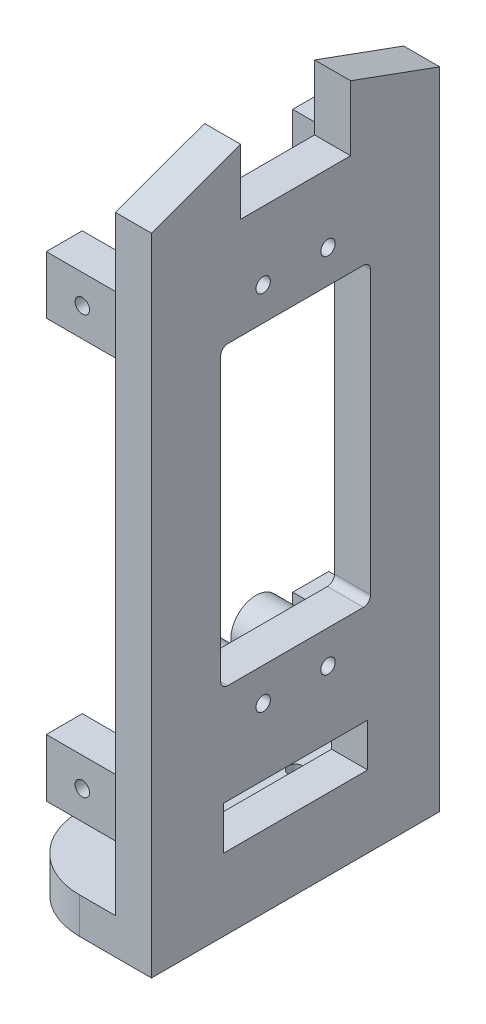
SolidWorks part; units mm, degrees
ref_plane "Front Plane" through (0, 0, 0) normal (0, 0, 1) x (1, 0, 0)
ref_plane "Top Plane" through (0, 0, 0) normal (0, 1, 0) x (1, 0, 0)
ref_plane "Right Plane" through (0, 0, 0) normal (1, 0, 0) x (0, 0, -1)
sketch "Sketch1" plane through (0, 0, 0) normal (0, 1, 0) x (1, 0, 0)
  line L0 (5.3196, -11.3329) -> (15.3196, -11.3329)
  line L1 (15.3196, -11.3329) -> (15.3196, 28.6671)
  line L2 (15.3196, 28.6671) -> (5.3196, 28.6671)
  line L3 (-4.6804, 18.6671) -> (-4.6804, -1.3329)
  arc A0 (5.3196, 28.6671) -> (-4.6804, 18.6671) centre (5.3196, 18.6671) ccw
  arc A1 (-4.6804, -1.3329) -> (5.3196, -11.3329) centre (5.3196, -1.3329) ccw
  circle A2 centre (5.3196, 18.6671) radius 1
  circle A3 centre (5.3196, -1.3329) radius 1
extrude "Boss-Extrude1" add sketch "Sketch1" along normal blind 5
sketch "Sketch2" plane through (0, 5, 0) normal (0, 1, 0) x (1, 0, 0)
  line L0 (15.3196, 28.6671) -> (15.3196, -11.3329)
  line L1 (15.3196, 28.6671) -> (10.3196, 28.6671)
  line L2 (15.3196, -11.3329) -> (10.3196, -11.3329)
  line L3 (10.3196, 28.6671) -> (10.3196, -11.3329)
  dimension "D1" = 5
extrude "Boss-Extrude2" add sketch "Sketch2" along normal blind 80
sketch "Sketch3" plane through (10.3196, 0, 0) normal (-1, 0, 0) x (0, 0, 1)
  line L0 (-8.6671, 85) -> (-8.6671, 5) construction
  line L1 (-28.6671, 85) -> (11.3329, 85) construction
  line L2 (-18.6671, 5) -> (1.3329, 5) construction
  line L4 (1.3329, 36.402) -> (1.3329, 60.5442)
  line L5 (-18.0671, 35.802) -> (0.7329, 35.802)
  line L7 (-18.6671, 60.5442) -> (-18.6671, 36.402)
  line L10 (-18.6671, 69.9442) -> (-18.6671, 60.5442)
  line L11 (-8.6671, 70.5442) -> (-12.0788, 70.5442)
  line L12 (-12.0788, 70.5442) -> (-18.0671, 70.5442)
  line L14 (-5.2553, 70.5442) -> (-8.6671, 70.5442)
  line L16 (0.7329, 70.5442) -> (-5.2553, 70.5442)
  line L17 (1.3329, 60.5442) -> (1.3329, 69.9442)
  line L19 (1.7329, 36.402) -> (1.7329, 60.5442)
  line L20 (1.7329, 60.5442) -> (1.7329, 69.9442)
  line L21 (0.7329, 70.9442) -> (-5.2553, 70.9442)
  line L22 (-5.2553, 70.9442) -> (-8.6671, 70.9442)
  line L23 (-8.6671, 70.9442) -> (-12.0788, 70.9442)
  line L24 (-12.0788, 70.9442) -> (-18.0671, 70.9442)
  line L25 (-19.0671, 69.9442) -> (-19.0671, 60.5442)
  line L26 (-19.0671, 60.5442) -> (-19.0671, 36.402)
  line L27 (-18.0671, 35.402) -> (0.7329, 35.402)
  arc A1 (0.7329, 35.802) -> (1.3329, 36.402) centre (0.7329, 36.402) ccw
  arc A2 (-18.6671, 36.402) -> (-18.0671, 35.802) centre (-18.0671, 36.402) ccw
  arc A5 (-18.0671, 70.5442) -> (-18.6671, 69.9442) centre (-18.0671, 69.9442) ccw
  arc A8 (1.3329, 69.9442) -> (0.7329, 70.5442) centre (0.7329, 69.9442) ccw
  arc A10 (-15.1231, 76.5942) -> (-11.2111, 76.5942) centre (-13.1671, 75.5442) ccw
  arc A11 (-11.2111, 24.1942) -> (-15.1231, 24.1942) centre (-13.1671, 25.2442) ccw
  arc A12 (-2.2111, 24.1942) -> (-6.1231, 24.1942) centre (-4.1671, 25.2442) ccw
  arc A13 (-6.1231, 76.5942) -> (-2.2111, 76.5942) centre (-4.1671, 75.5442) ccw
  arc A14 (1.7329, 69.9442) -> (0.7329, 70.9442) centre (0.7329, 69.9442) ccw
  arc A15 (-18.0671, 70.9442) -> (-19.0671, 69.9442) centre (-18.0671, 69.9442) ccw
  arc A16 (-19.0671, 36.402) -> (-18.0671, 35.402) centre (-18.0671, 36.402) ccw
  arc A17 (0.7329, 35.402) -> (1.7329, 36.402) centre (0.7329, 36.402) ccw
  circle A18 centre (-13.1671, 25.2442) radius 2.22
  circle A19 centre (-4.1671, 25.2442) radius 2.22
  circle A20 centre (-13.1671, 75.5442) radius 2.22
  circle A21 centre (-4.1671, 75.5442) radius 2.22
  dimension "D1" = 0.4
extrude "Cut-Extrude3" cut sketch "Sketch3" against normal blind 80 contours A12 A19 | A11 A18 | L0 L11 L12 A5 L10 L7 A2 L5 | L14 L0 L5 A1 L4 L17 A8 L16 | L0 L23 L24 A15 L25 L26 A16 L27 L5 A2 L7 L10 A5 L12 L11 | L22 L0 L14 L16 A8 L17 L4 A1 L5 L27 A17 L19 L20 A14 L21 | A13 A21 | A10 A20
sketch "Sketch5" plane through (15.3196, 0, 0) normal (1, 0, 0) x (0, 0, -1)
  circle A0 centre (4.1671, 25.2442) radius 2.22 construction
  circle A1 centre (13.1671, 25.2442) radius 2.22 construction
  circle A2 centre (4.1671, 75.5442) radius 2.22 construction
  circle A3 centre (13.1671, 75.5442) radius 2.22 construction
  circle A4 centre (4.1671, 25.2442) radius 2.22
  circle A5 centre (13.1671, 25.2442) radius 2.22
  circle A6 centre (4.1671, 75.5442) radius 2.22
  circle A7 centre (13.1671, 75.5442) radius 2.22
  circle A8 centre (4.1671, 75.5442) radius 1
  circle A9 centre (13.1671, 75.5442) radius 1
  circle A10 centre (13.1671, 25.2442) radius 1
  circle A11 centre (4.1671, 25.2442) radius 1
  dimension "D1" = 2
  dimension "D2" = 2
  dimension "D3" = 2
  dimension "D4" = 2
extrude "Boss-Extrude3" add sketch "Sketch5" against normal blind 10
sketch "Sketch6" plane through (10.3196, 0, 0) normal (-1, 0, 0) x (0, 0, 1)
  circle A0 centre (-4.1671, 25.2442) radius 3.5
  circle A1 centre (-13.1671, 25.2442) radius 3.5
  circle A2 centre (-4.1671, 75.5442) radius 3.5
  circle A3 centre (-13.1671, 75.5442) radius 3.5
  circle A4 centre (-13.1671, 25.2442) radius 2.22 construction
  circle A5 centre (-4.1671, 25.2442) radius 2.22 construction
  circle A6 centre (-4.1671, 75.5442) radius 2.22 construction
  circle A7 centre (-13.1671, 75.5442) radius 2.22 construction
  circle A8 centre (-13.1671, 25.2442) radius 2.22
  circle A9 centre (-4.1671, 25.2442) radius 2.22
  circle A10 centre (-4.1671, 75.5442) radius 2.22
  circle A11 centre (-13.1671, 75.5442) radius 2.22
  dimension "D1" = 7
extrude "Boss-Extrude4" add sketch "Sketch6" along normal up to surface (5 mm away) up to face at (5.3196, 25.2442, -5.1671)
sketch "Sketch7" plane through (10.3196, 0, 0) normal (-1, 0, 0) x (0, 0, 1)
  line L0 (0.7329, 57.1325) -> (0.7329, 36.402)
  line L1 (1.3329, 36.402) -> (1.3329, 60.5442)
  line L2 (-18.0671, 35.802) -> (0.7329, 35.802)
  line L3 (0.7329, 36.402) -> (-18.0671, 36.402)
  line L4 (-18.6671, 60.5442) -> (-18.6671, 36.402)
  line L5 (-18.0671, 36.402) -> (-18.0671, 57.1325)
  line L6 (-18.0671, 63.9559) -> (-18.0671, 69.9442)
  line L7 (-18.6671, 69.9442) -> (-18.6671, 60.5442)
  line L8 (-8.6671, 70.5442) -> (-12.0788, 70.5442)
  line L9 (-12.0788, 70.5442) -> (-18.0671, 70.5442)
  line L10 (-18.0671, 69.9442) -> (-12.0788, 69.9442)
  line L11 (-5.2553, 70.5442) -> (-8.6671, 70.5442)
  line L12 (-5.2553, 69.9442) -> (0.7329, 69.9442)
  line L13 (0.7329, 70.5442) -> (-5.2553, 70.5442)
  line L14 (1.3329, 60.5442) -> (1.3329, 69.9442)
  line L15 (0.7329, 69.9442) -> (0.7329, 63.9559)
  line L16 (-18.0671, 30.8442) -> (-18.0671, 35.802)
  line L17 (-18.6671, 36.402) -> (-18.6671, 30.8442)
  line L18 (1.3329, 30.8442) -> (1.3329, 36.402)
  line L19 (0.7329, 35.802) -> (0.7329, 30.8442)
  line L20 (-18.0671, 30.2442) -> (0.7329, 30.2442)
  line L21 (0.7329, 30.8442) -> (-18.0671, 30.8442)
  line L22 (-19.0671, 36.402) -> (-19.0671, 30.8442)
  line L23 (-18.0671, 29.8442) -> (0.7329, 29.8442)
  line L24 (1.7329, 30.8442) -> (1.7329, 36.402)
  line L25 (-18.0671, 35.402) -> (0.7329, 35.402) construction
  line L26 (-18.0671, 35.402) -> (0.7329, 35.402)
  arc A0 (1.1801, 58.8028) -> (1.3329, 60.5442) centre (-8.6671, 60.5442) ccw
  arc A1 (0.7329, 35.802) -> (1.3329, 36.402) centre (0.7329, 36.402) ccw
  arc A2 (-18.6671, 36.402) -> (-18.0671, 35.802) centre (-18.0671, 36.402) ccw
  arc A3 (-18.6671, 60.5442) -> (-18.5143, 58.8028) centre (-8.6671, 60.5442) ccw
  arc A4 (-18.0671, 63.9559) -> (-18.6671, 60.5442) centre (-8.6671, 60.5442) ccw
  arc A5 (-18.0671, 70.5442) -> (-18.6671, 69.9442) centre (-18.0671, 69.9442) ccw
  arc A6 (-8.6671, 70.5442) -> (-12.0788, 69.9442) centre (-8.6671, 60.5442) ccw
  arc A7 (-5.2553, 69.9442) -> (-8.6671, 70.5442) centre (-8.6671, 60.5442) ccw
  arc A8 (1.3329, 69.9442) -> (0.7329, 70.5442) centre (0.7329, 69.9442) ccw
  arc A9 (1.3329, 60.5442) -> (0.7329, 63.9559) centre (-8.6671, 60.5442) ccw
  arc A10 (-15.1231, 76.5942) -> (-11.2111, 76.5942) centre (-13.1671, 75.5442) ccw
  arc A11 (-19.0671, 30.8442) -> (-18.0671, 29.8442) centre (-18.0671, 30.8442) ccw
  arc A12 (0.7329, 29.8442) -> (1.7329, 30.8442) centre (0.7329, 30.8442) ccw
  arc A13 (-6.1231, 76.5942) -> (-2.2111, 76.5942) centre (-4.1671, 75.5442) ccw
  arc A14 (-18.6671, 36.402) -> (-18.0671, 35.802) centre (-18.0671, 36.402) ccw
  arc A15 (-18.6671, 30.8442) -> (-18.0671, 30.2442) centre (-18.0671, 30.8442) ccw
  arc A16 (0.7329, 35.802) -> (1.3329, 36.402) centre (0.7329, 36.402) ccw
  arc A17 (0.7329, 30.2442) -> (1.3329, 30.8442) centre (0.7329, 30.8442) ccw
  circle A18 centre (-13.1671, 75.5442) radius 1 construction
  circle A19 centre (-13.1671, 75.5442) radius 1
  arc A20 (0.7329, 35.402) -> (1.7329, 36.402) centre (0.7329, 36.402) ccw construction
  arc A21 (-19.0671, 36.402) -> (-18.0671, 35.402) centre (-18.0671, 36.402) ccw construction
  arc A22 (0.7329, 35.402) -> (1.7329, 36.402) centre (0.7329, 36.402) ccw
  arc A23 (-19.0671, 36.402) -> (-18.0671, 35.402) centre (-18.0671, 36.402) ccw
  spline S0 degree 3 poles (1.1801, 58.8028) (1.1306, 58.5225) (1.0683, 58.2411) (0.9193, 57.6834) (0.8326, 57.4071) (0.7329, 57.1325) knots 0 0 0 0 0.5 0.5 1 1 1 1
  spline S1 degree 3 poles (-18.0671, 57.1325) (-18.1668, 57.4071) (-18.2535, 57.6834) (-18.4025, 58.2411) (-18.4647, 58.5225) (-18.5143, 58.8028) knots 0 0 0 0 0.5 0.5 1 1 1 1
  arc M9 (1.7329, 36.402) -> (0.7329, 35.402) centre (0.7329, 36.402) cw
  line M10 (0.7329, 35.402) -> (-18.0671, 35.402)
  arc M11 (-18.0671, 35.402) -> (-19.0671, 36.402) centre (-18.0671, 36.402) cw
  dimension "D1" = 0.4
extrude "Cut-Extrude4" cut sketch "Sketch7" against normal blind 10 contours A17 L20 A15 L17 L22 A11 L23 A12 L24 L18 M11 M9 | L20 A17 L18 L19 L21 L16 L17 A15 M9 M11 | L21 L19 L16 M10
sketch "Sketch8" plane through (10.3196, 0, 0) normal (-1, 0, 0) x (0, 0, 1)
  line L0 (-28.6671, 85) -> (-28.6671, 89.5078)
  line L1 (-28.6671, 85) -> (11.3329, 85)
  line L2 (11.3329, 89.5078) -> (11.3329, 85)
  line L3 (-28.6671, 85) -> (11.3329, 85) construction
  line L4 (-16.3005, 85) -> (-1.0337, 85)
  line L5 (-16.3005, 85) -> (-16.3005, 94.0156)
  line L7 (-1.0337, 85) -> (-1.0337, 94.0156)
  line L10 (-28.6671, 89.5078) -> (-16.3005, 94.0156)
  line L11 (-1.0337, 94.0156) -> (11.3329, 89.5078)
  point P3 (-8.6671, 89.5078)
  line M14 (11.3329, 85) -> (-28.6671, 85)
extrude "Boss-Extrude5" add sketch "Sketch8" against normal through all contours L10 L0 L5 M14 | L11 L7 L2 M14
sketch "Sketch9" plane through (10.3196, 0, 0) normal (-1, 0, 0) x (0, 0, 1)
  line L0 (-18.6671, 5) -> (-18.6671, 10)
  line L1 (-18.6671, 10) -> (1.3329, 10)
  line L2 (1.3329, 10) -> (1.3329, 5)
  line L3 (-18.6671, 16) -> (-18.6671, 10)
  line L4 (-18.6671, 0) -> (1.3329, 0)
  line L5 (1.3329, 0) -> (1.3329, 5)
  line L6 (1.3329, 5) -> (-18.6671, 5)
  line L7 (-18.6671, 5) -> (-18.6671, 0)
  line L8 (-18.6671, 0) -> (1.3329, 0)
  line L9 (1.3329, 0) -> (1.3329, 5)
  line L10 (1.3329, 5) -> (-18.6671, 5)
  line L11 (-18.6671, 5) -> (-18.6671, 0)
  line L12 (-18.6671, 16) -> (1.3329, 16)
  line L13 (-18.6671, 10) -> (1.3329, 10)
  line L14 (1.3329, 16) -> (1.3329, 10)
  dimension "D2" = 5
  dimension "D3" = 6
  dimension "D1" = 0
extrude "Cut-Extrude7" cut sketch "Sketch9" against normal blind 10 contours L14 L12 L3 L1
sketch "Sketch10" plane through (10.3196, 0, 0) normal (-1, 0, 0) x (0, 0, 1)
  line L0 (-28.2671, 5.4) -> (10.9329, 5.4)
  line L1 (10.9329, 5.4) -> (10.9329, 89.2279)
  line L2 (10.9329, 89.2279) -> (-0.6337, 93.444)
  line L3 (-0.6337, 93.444) -> (-0.6337, 84.6)
  line L4 (-0.6337, 84.6) -> (-16.7005, 84.6)
  line L5 (-16.7005, 84.6) -> (-16.7005, 93.444)
  line L6 (-16.7005, 93.444) -> (-28.2671, 89.2279)
  line L7 (-28.2671, 89.2279) -> (-28.2671, 5.4)
  line L8 (-28.6671, 5) -> (11.3329, 5)
  line L9 (11.3329, 5) -> (11.3329, 89.5078)
  line L10 (11.3329, 89.5078) -> (-1.0337, 94.0156)
  line L11 (-1.0337, 94.0156) -> (-1.0337, 85)
  line L12 (-1.0337, 85) -> (-16.3005, 85)
  line L13 (-16.3005, 85) -> (-16.3005, 94.0156)
  line L14 (-16.3005, 94.0156) -> (-28.6671, 89.5078)
  line L15 (-28.6671, 89.5078) -> (-28.6671, 5)
  line L16 (-28.6671, 5) -> (11.3329, 5)
  line L17 (11.3329, 5) -> (11.3329, 89.5078)
  line L18 (11.3329, 89.5078) -> (-1.0337, 94.0156)
  line L19 (-1.0337, 94.0156) -> (-1.0337, 85)
  line L20 (-1.0337, 85) -> (-16.3005, 85)
  line L21 (-16.3005, 85) -> (-16.3005, 94.0156)
  line L22 (-16.3005, 94.0156) -> (-28.6671, 89.5078)
  line L23 (-28.6671, 89.5078) -> (-28.6671, 5)
  line L24 (-28.2671, 5.4) -> (-23.2671, 5.4)
  line L25 (-28.2671, 5.4) -> (-28.2671, 13.5669)
  line L26 (-23.2671, 5.4) -> (-23.2671, 13.5669)
  line L27 (-28.2671, 13.5669) -> (-23.2671, 13.5669)
  line L28 (-28.2671, 13.5669) -> (-23.2671, 13.5669)
  line L29 (-28.2671, 13.5669) -> (-28.2671, 21.5669)
  line L30 (-23.2671, 13.5669) -> (-23.2671, 21.5669)
  line L31 (-28.2671, 21.5669) -> (-23.2671, 21.5669)
  line L32 (-28.2671, 84.6) -> (-23.2671, 84.6)
  line L33 (-28.2671, 84.6) -> (-28.2671, 79.6)
  line L34 (-23.2671, 84.6) -> (-23.2671, 79.6)
  line L35 (-28.2671, 79.6) -> (-23.2671, 79.6)
  line L36 (-28.2671, 79.6) -> (-23.2671, 79.6)
  line L37 (-28.2671, 79.6) -> (-28.2671, 71.6)
  line L38 (-23.2671, 79.6) -> (-23.2671, 71.6)
  line L39 (-28.2671, 71.6) -> (-23.2671, 71.6)
  line L40 (-8.6671, 84.6) -> (-8.6671, 5.4) construction
  line L41 (10.9329, 71.6) -> (5.9329, 71.6)
  line L42 (5.9329, 79.6) -> (5.9329, 71.6)
  line L43 (10.9329, 79.6) -> (10.9329, 71.6)
  line L44 (10.9329, 79.6) -> (5.9329, 79.6)
  line L45 (10.9329, 79.6) -> (5.9329, 79.6)
  line L46 (5.9329, 84.6) -> (5.9329, 79.6)
  line L47 (10.9329, 84.6) -> (10.9329, 79.6)
  line L48 (10.9329, 84.6) -> (5.9329, 84.6)
  line L49 (10.9329, 21.5669) -> (5.9329, 21.5669)
  line L50 (5.9329, 13.5669) -> (5.9329, 21.5669)
  line L51 (10.9329, 13.5669) -> (10.9329, 21.5669)
  line L52 (10.9329, 13.5669) -> (5.9329, 13.5669)
  line L53 (10.9329, 13.5669) -> (5.9329, 13.5669)
  line L54 (5.9329, 5.4) -> (5.9329, 13.5669)
  line L55 (10.9329, 5.4) -> (10.9329, 13.5669)
  line L56 (10.9329, 5.4) -> (5.9329, 5.4)
  line L57 (11.3329, 89.5078) -> (11.3329, 5)
  line L58 (-1.0337, 94.0156) -> (11.3329, 89.5078)
  line L59 (10.9329, 89.2279) -> (10.9329, 5.4)
  line L60 (-0.6337, 93.444) -> (10.9329, 89.2279)
  line L61 (-0.6337, 84.6) -> (-0.6337, 93.444)
  dimension "D3" = 5
  dimension "D4" = 8
  dimension "D5" = 5
  dimension "D6" = 8
  dimension "D1" = 0
  dimension "D2" = 0.4
extrude "Boss-Extrude6" add sketch "Sketch10" along normal blind 10 contours L31 L7 L27 L30 | L52 L1 L49 L50 | L1 L44 L42 L41 | L7 L39 L38 L35
sketch "Sketch11" plane through (0, 0, 10.9329) normal (0, 0, 1) x (1, 0, 0)
  line L0 (0.3196, 79.6) -> (10.3196, 71.6) construction
  line L1 (10.3196, 71.6) -> (10.3196, 21.5669) construction
  line L2 (10.3196, 21.5669) -> (0.3196, 13.5669) construction
  circle A0 centre (5.3196, 17.5669) radius 1
  circle A1 centre (5.3196, 75.6) radius 1
  dimension "D1" = 2
  dimension "D2" = 2
extrude "Cut-Extrude9" cut sketch "Sketch11" against normal blind 8
sketch "Sketch12" plane through (0, 0, -28.2671) normal (0, 0, -1) x (-1, 0, 0)
  circle A0 centre (-5.3196, 75.6) radius 1 construction
  circle A1 centre (-5.3196, 17.5669) radius 1 construction
  circle A2 centre (-5.3196, 75.6) radius 1
  circle A3 centre (-5.3196, 17.5669) radius 1
extrude "Cut-Extrude10" cut sketch "Sketch12" against normal blind 8
